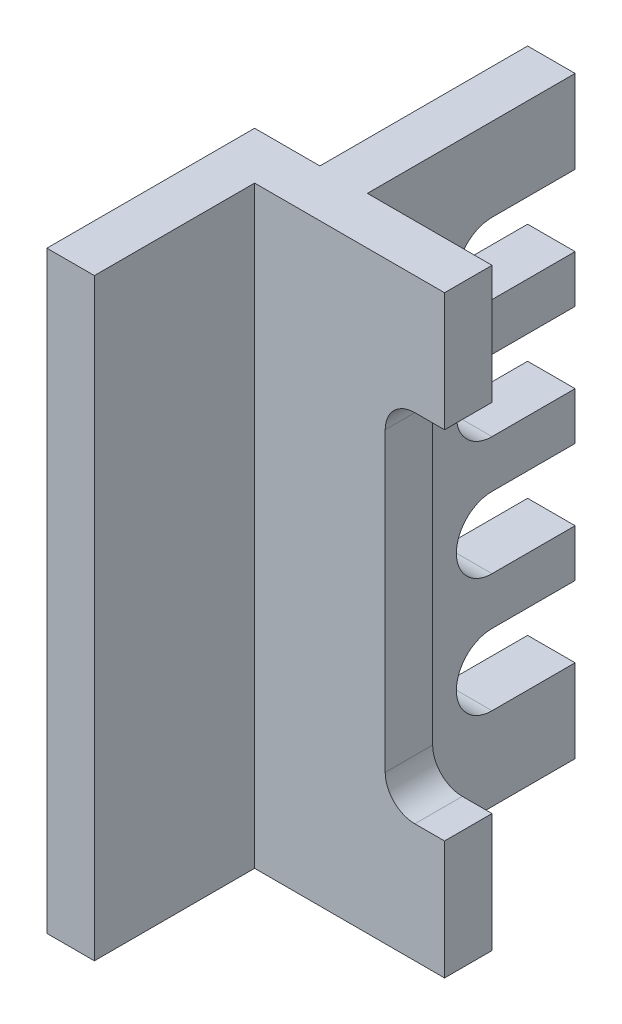
SolidWorks part; units mm, degrees
ref_plane "Front Plane" through (0, 0, 0) normal (0, 0, 1) x (1, 0, 0)
ref_plane "Top Plane" through (0, 0, 0) normal (0, 1, 0) x (1, 0, 0)
ref_plane "Right Plane" through (0, 0, 0) normal (1, 0, 0) x (0, 0, -1)
sketch "Sketch1" plane through (0, 0, 0) normal (0, 1, 0) x (1, 0, 0)
  line L0 (0, 0) -> (8, 0)
  line L1 (8, 0) -> (8, 27)
  line L2 (8, 27) -> (40, 27)
  line L3 (40, 27) -> (40, 35)
  line L4 (40, 35) -> (0, 35)
  line L5 (0, 35) -> (0, 0)
  dimension "D1" = 8
  dimension "D2" = 40
  dimension "D3" = 35
  dimension "D4" = 8
extrude "Boss-Extrude1" add sketch "Sketch1" along normal blind 100
sketch "Sketch3" plane through (0, 0, -35) normal (0, 0, -1) x (-1, 0, 0)
  line L0 (-40, 20) -> (-35, 20)
  line L1 (-40, 100) -> (-40, 0) construction
  line L2 (-30, 25) -> (-30, 75)
  line L3 (-35, 80) -> (-40, 80)
  line L4 (-40, 80) -> (-40, 20)
  arc A0 (-35, 80) -> (-30, 75) centre (-35, 75) cw
  arc A1 (-35, 20) -> (-30, 25) centre (-35, 25) ccw
  point P11 (-30, 20)
  dimension "D4" = 5
  dimension "D5" = 5
  dimension "D1" = 20
  dimension "D2" = 60
  dimension "D3" = 10
extrude "Cut-Extrude1" cut sketch "Sketch3" against normal blind 8
sketch "Sketch4" plane through (0, 0, -35) normal (0, 0, -1) x (-1, 0, 0)
  line L0 (-19, 100) -> (-19, 0)
  line L1 (-40, 100) -> (0, 100) construction
  line L2 (-40, 0) -> (0, 0) construction
  line L3 (-19, 0) -> (-11, 0)
  line L4 (-11, 0) -> (-11, 100)
  line L5 (-11, 100) -> (-19, 100)
  dimension "D1" = 21
  dimension "D2" = 8
extrude "Boss-Extrude2" add sketch "Sketch4" along normal blind 35
sketch "Sketch5" plane through (19, 0, 0) normal (1, 0, 0) x (0, 0, -1)
  line L0 (70, 100) -> (70, 0) construction
  line L1 (56, 86) -> (70, 86)
  line L2 (70, 86) -> (70, 74)
  line L3 (70, 74) -> (56, 74)
  line L4 (70, 54) -> (56, 54)
  line L5 (70, 66) -> (70, 54)
  line L6 (56, 66) -> (70, 66)
  line L7 (70, 34) -> (56, 34)
  line L8 (70, 46) -> (70, 34)
  line L9 (56, 46) -> (70, 46)
  line L10 (70, 14) -> (56, 14)
  line L11 (70, 26) -> (70, 14)
  line L12 (56, 26) -> (70, 26)
  arc A0 (56, 86) -> (56, 74) centre (56, 80) ccw
  arc A1 (56, 66) -> (56, 54) centre (56, 60) ccw
  arc A2 (56, 46) -> (56, 34) centre (56, 40) ccw
  arc A3 (56, 26) -> (56, 14) centre (56, 20) ccw
  dimension "D2" = 12
  dimension "D1" = 14
  dimension "D3" = 20
  dimension "D5" = 20
  dimension "D4" = 4
extrude "Cut-Extrude2" cut sketch "Sketch5" against normal blind 8
